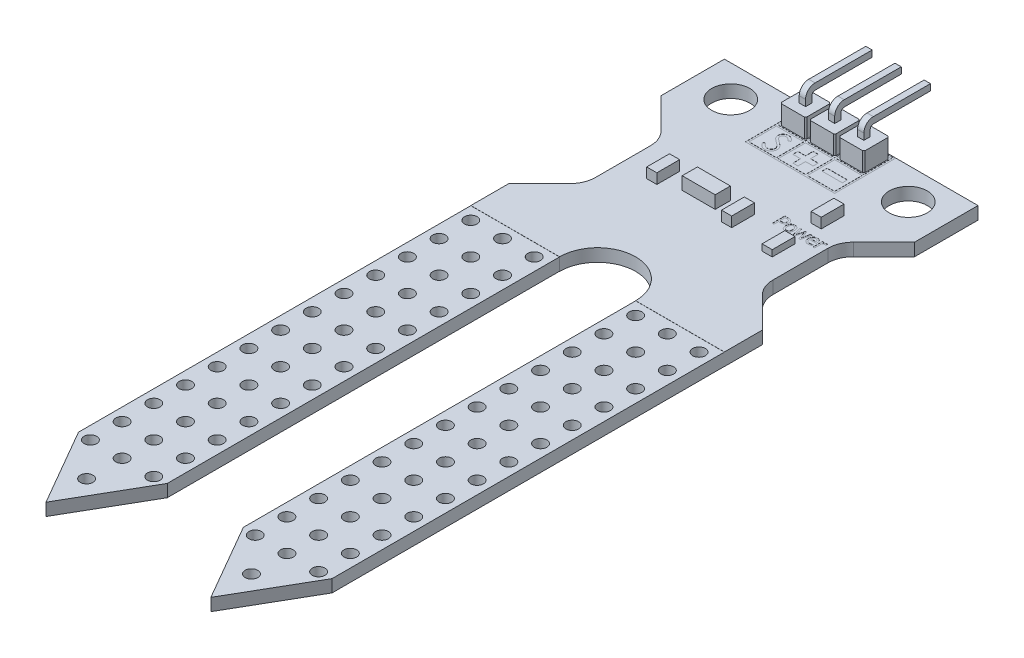
SolidWorks part; units mm, degrees
other "Camera2"
other "Camera4"
ref_plane "Front Plane" through (0, 0, 0) normal (0, 0, 1) x (1, 0, 0)
ref_plane "Top Plane" through (0, 0, 0) normal (0, 1, 0) x (1, 0, 0)
ref_plane "Right Plane" through (0, 0, 0) normal (1, 0, 0) x (0, 0, -1)
sketch "Sketch1" plane through (0, 0, 0) normal (0, 1, 0) x (1, 0, 0)
  line L0 (-10, 0) -> (10, 0)
  line L1 (-10, 0) -> (-10, -57) construction
  line L2 (-10, -57) -> (10, -57) construction
  line L3 (10, -57) -> (10, 0) construction
  line L4 (-10, 0) -> (-10, -5)
  line L5 (-10, -5) -> (-7.5858, -7.4142)
  line L6 (-7, -8.8284) -> (-7, -13.1716)
  line L7 (-7, -11) -> (-10, -11) construction
  line L8 (-10, -17) -> (-7.5858, -14.5858)
  line L9 (-7, -2.5) -> (7, -2.5) construction
  line L10 (0, 0) -> (0, -2.5) construction
  line L11 (-10, -17) -> (-10, -20)
  line L12 (-10, -20) -> (-3, -20)
  line L13 (10, 0) -> (10, -5)
  line L14 (7, -11) -> (10, -11) construction
  line L15 (10, -20) -> (3, -20)
  line L16 (10, -17) -> (10, -20)
  line L17 (10, -17) -> (7.5858, -14.5858)
  line L18 (7, -8.8284) -> (7, -13.1716)
  line L19 (10, -5) -> (7.5858, -7.4142)
  arc A0 (-7.5858, -7.4142) -> (-7, -8.8284) centre (-9, -8.8284) cw
  arc A1 (-7.5858, -14.5858) -> (-7, -13.1716) centre (-9, -13.1716) ccw
  arc A2 (7.5858, -14.5858) -> (7, -13.1716) centre (9, -13.1716) cw
  arc A3 (7.5858, -7.4142) -> (7, -8.8284) centre (9, -8.8284) ccw
  arc A4 (-3, -20) -> (3, -20) centre (0, -20) cw
  point P4 (0, 0)
  point P19 (0, -2.5)
  point P21 (-10, -2.5)
  dimension "D4" = 14
  dimension "D7" = 2
  dimension "D1" = 20
  dimension "D2" = 57
  dimension "D3" = 5
  dimension "D5" = 12
  dimension "D6" = 45
  dimension "D8" = 3
  dimension "D9" = 7
extrude "Base" add sketch "Sketch1" along normal mid plane 1
sketch "Sketch2" plane through (0, 0.5, 0) normal (0, 1, 0) x (1, 0, 0)
  line L0 (0, 0) -> (0, -17) construction
  line L1 (10, 0) -> (-10, 0) construction
  line L2 (7, -2.5) -> (-7, -2.5) construction
  circle A0 centre (-7, -2.5) radius 1.5
  arc A1 (3, -20) -> (-3, -20) centre (0, -20) ccw construction
  circle A2 centre (7, -2.5) radius 1.5
  point P12 (0, -2.5)
  dimension "D1" = 3
  dimension "D3" = 2.5
  dimension "D2" = 14
extrude "Holes" cut sketch "Sketch2" against normal up to next
sketch "Sketch3" plane through (0, 0, 0) normal (0, 1, 0) x (1, 0, 0)
  line L0 (0, 0) -> (0, -57) construction
  line L1 (-10, -20) -> (-3, -20)
  line L2 (-10, -20) -> (-10, -50.9378)
  line L3 (-10, -50.9378) -> (-6.5, -57)
  line L4 (-6.5, -57) -> (-3, -50.9378)
  line L5 (-3, -50.9378) -> (-3, -20)
  line L6 (-6.5, -20) -> (-6.5, -57) construction
  line L7 (-10, -50.9378) -> (-3, -50.9378) construction
  line L8 (10, -50.9378) -> (3, -50.9378) construction
  line L9 (6.5, -20) -> (6.5, -57) construction
  line L10 (3, -50.9378) -> (3, -20)
  line L11 (6.5, -57) -> (3, -50.9378)
  line L12 (10, -50.9378) -> (6.5, -57)
  line L13 (10, -20) -> (10, -50.9378)
  line L14 (10, -20) -> (3, -20)
  dimension "D1" = 57
  dimension "D2" = 30
extrude "Plate" add sketch "Sketch3" along normal mid plane 0.98
sketch "Sketch4" plane through (0, 0.49, 0) normal (0, 1, 0) x (1, 0, 0)
  line L0 (-9, -21) -> (-4, -21) construction
  line L1 (-9, -21) -> (-9, -23.5) construction
  line L2 (-9, -23.5) -> (-6.5, -23.5) construction
  line L3 (-6.5, -51) -> (-6.5, -53.8) construction
  line L4 (-6.5, -20) -> (-6.5, -21) construction
  line L5 (-3, -20) -> (-10, -20) construction
  line L6 (0, 72.5532) -> (0, -72.5532) construction
  line L7 (6.5, -20) -> (6.5, -21) construction
  line L8 (6.5, -51) -> (6.5, -53.8) construction
  line L9 (9, -23.5) -> (6.5, -23.5) construction
  line L10 (9, -21) -> (9, -23.5) construction
  line L11 (9, -21) -> (4, -21) construction
  circle A0 centre (-9, -21) radius 0.5
  circle A1 centre (-6.5, -21) radius 0.5
  circle A2 centre (-4, -21) radius 0.5
  circle A3 centre (-6.5, -23.5) radius 0.5
  circle A4 centre (-4, -23.5) radius 0.5
  circle A5 centre (-6.5, -26) radius 0.5
  circle A6 centre (-4, -26) radius 0.5
  circle A7 centre (-6.5, -28.5) radius 0.5
  circle A8 centre (-4, -28.5) radius 0.5
  circle A9 centre (-6.5, -31) radius 0.5
  circle A10 centre (-4, -31) radius 0.5
  circle A11 centre (-6.5, -33.5) radius 0.5
  circle A12 centre (-4, -33.5) radius 0.5
  circle A13 centre (-6.5, -36) radius 0.5
  circle A14 centre (-4, -36) radius 0.5
  circle A15 centre (-6.5, -38.5) radius 0.5
  circle A16 centre (-4, -38.5) radius 0.5
  circle A17 centre (-6.5, -41) radius 0.5
  circle A18 centre (-4, -41) radius 0.5
  circle A19 centre (-6.5, -43.5) radius 0.5
  circle A20 centre (-4, -43.5) radius 0.5
  circle A21 centre (-6.5, -46) radius 0.5
  circle A22 centre (-4, -46) radius 0.5
  circle A23 centre (-6.5, -48.5) radius 0.5
  circle A24 centre (-4, -48.5) radius 0.5
  circle A25 centre (-6.5, -51) radius 0.5
  circle A26 centre (-4, -51) radius 0.5
  circle A27 centre (-9, -23.5) radius 0.5
  circle A28 centre (-9, -26) radius 0.5
  circle A29 centre (-9, -28.5) radius 0.5
  circle A30 centre (-9, -31) radius 0.5
  circle A31 centre (-9, -33.5) radius 0.5
  circle A32 centre (-9, -36) radius 0.5
  circle A33 centre (-9, -38.5) radius 0.5
  circle A34 centre (-9, -41) radius 0.5
  circle A35 centre (-9, -43.5) radius 0.5
  circle A36 centre (-9, -46) radius 0.5
  circle A37 centre (-9, -48.5) radius 0.5
  circle A38 centre (-9, -51) radius 0.5
  circle A39 centre (-6.5, -53.8) radius 0.5
  circle A40 centre (6.5, -53.8) radius 0.5
  circle A41 centre (9, -51) radius 0.5
  circle A42 centre (9, -48.5) radius 0.5
  circle A43 centre (9, -46) radius 0.5
  circle A44 centre (9, -43.5) radius 0.5
  circle A45 centre (9, -41) radius 0.5
  circle A46 centre (9, -38.5) radius 0.5
  circle A47 centre (9, -36) radius 0.5
  circle A48 centre (9, -33.5) radius 0.5
  circle A49 centre (9, -31) radius 0.5
  circle A50 centre (9, -28.5) radius 0.5
  circle A51 centre (9, -26) radius 0.5
  circle A52 centre (9, -23.5) radius 0.5
  circle A53 centre (4, -51) radius 0.5
  circle A54 centre (6.5, -51) radius 0.5
  circle A55 centre (4, -48.5) radius 0.5
  circle A56 centre (6.5, -48.5) radius 0.5
  circle A57 centre (4, -46) radius 0.5
  circle A58 centre (6.5, -46) radius 0.5
  circle A59 centre (4, -43.5) radius 0.5
  circle A60 centre (6.5, -43.5) radius 0.5
  circle A61 centre (4, -41) radius 0.5
  circle A62 centre (6.5, -41) radius 0.5
  circle A63 centre (4, -38.5) radius 0.5
  circle A64 centre (6.5, -38.5) radius 0.5
  circle A65 centre (4, -36) radius 0.5
  circle A66 centre (6.5, -36) radius 0.5
  circle A67 centre (4, -33.5) radius 0.5
  circle A68 centre (6.5, -33.5) radius 0.5
  circle A69 centre (4, -31) radius 0.5
  circle A70 centre (6.5, -31) radius 0.5
  circle A71 centre (4, -28.5) radius 0.5
  circle A72 centre (6.5, -28.5) radius 0.5
  circle A73 centre (4, -26) radius 0.5
  circle A74 centre (6.5, -26) radius 0.5
  circle A75 centre (4, -23.5) radius 0.5
  circle A76 centre (6.5, -23.5) radius 0.5
  circle A77 centre (4, -21) radius 0.5
  circle A78 centre (6.5, -21) radius 0.5
  circle A79 centre (9, -21) radius 0.5
  point P89 (0, 0)
  dimension "D1" = 1
  dimension "D8" = 2.8
  dimension "D2" = 5
  dimension "D3" = 1
  dimension "D6" = 2.5
  dimension "D4" = 3
  dimension "D5" = 13
extrude "Plate holes" cut sketch "Sketch4" against normal through all
sketch "Sketch5" plane through (0, 0.5, 0) normal (0, 1, 0) x (1, 0, 0)
  line L0 (-7, -2.5) -> (7, -2.5) construction
  line L1 (-3.2, -0.3) -> (-3.3, -0.4)
  line L2 (-3.2, -0.3) -> (-1.4, -0.3)
  line L3 (-3.3, -0.4) -> (-3.3, -2.2)
  line L4 (-3.2, -2.3) -> (-1.4, -2.3)
  line L5 (-1.3, -0.4) -> (-1.3, -2.2)
  line L6 (-3.3, -0.3) -> (-1.3, -2.3) construction
  line L7 (-3.3, -2.3) -> (-1.3, -0.3) construction
  line L8 (-1.4, -0.3) -> (-1.3, -0.4)
  line L9 (-3.3, -2.2) -> (-3.2, -2.3)
  line L10 (-1.3, -2.2) -> (-1.4, -2.3)
  line L11 (-0.9, -0.3) -> (-1, -0.4)
  line L12 (-0.9, -0.3) -> (0.9, -0.3)
  line L13 (-1, -0.4) -> (-1, -2.2)
  line L14 (-0.9, -2.3) -> (0.9, -2.3)
  line L15 (1, -0.4) -> (1, -2.2)
  line L16 (0.9, -0.3) -> (1, -0.4)
  line L17 (-1, -2.2) -> (-0.9, -2.3)
  line L18 (1, -2.2) -> (0.9, -2.3)
  line L19 (-1, -0.3) -> (1, -2.3) construction
  line L20 (-1, -2.3) -> (1, -0.3) construction
  line L21 (1.4, -0.3) -> (1.3, -0.4)
  line L22 (1.4, -0.3) -> (3.2, -0.3)
  line L23 (1.3, -0.4) -> (1.3, -2.2)
  line L24 (1.4, -2.3) -> (3.2, -2.3)
  line L25 (3.3, -0.4) -> (3.3, -2.2)
  line L26 (3.2, -0.3) -> (3.3, -0.4)
  line L27 (1.3, -2.2) -> (1.4, -2.3)
  line L28 (3.3, -2.2) -> (3.2, -2.3)
  line L29 (1.3, -0.3) -> (3.3, -2.3) construction
  line L30 (1.3, -2.3) -> (3.3, -0.3) construction
  line L31 (0, -2.3) -> (0, -2.5) construction
  point P4 (-2.3, -1.3)
  point P19 (0, -1.3)
  point P32 (2.3, -1.3)
  dimension "D1" = 2
  dimension "D2" = 3
  dimension "D3" = 0.2
  dimension "D8" = 0.3
extrude "Socket" add sketch "Sketch5" along normal blind 1.5
sketch "Sketch6" plane through (0, 2, 0) normal (0, 1, 0) x (1, 0, 0)
  line L0 (-2.3, -1.3) -> (-2.3, -0.3) construction
  line L1 (-2.6, -1.6) -> (-2, -1.6)
  line L2 (-2.6, -1.6) -> (-2.6, -1)
  line L3 (-2.6, -1) -> (-2, -1)
  line L4 (-2, -1.6) -> (-2, -1)
  line L5 (-2.6, -1.6) -> (-2, -1) construction
  line L6 (-2.6, -1) -> (-2, -1.6) construction
  line L8 (-1.4, -0.3) -> (-3.2, -0.3) construction
  line L9 (-2.3, -1.3) -> (-3.3, -1.3) construction
  line L10 (-3.3, -0.4) -> (-3.3, -2.2) construction
  point P0 (-2.3, -1.3)
  dimension "D1" = 0.6
sketch "Sketch7" plane through (0, 0, 0) normal (1, 0, 0) x (0, 0, -1)
  line L0 (-1.3, 2) -> (-1.3, 2.5) construction
  line L1 (-0.4, 2) -> (-2.2, 2) construction
  line L2 (-0.8, 3) -> (3.7, 3) construction
  line L3 (-1.05, 2) -> (-1.05, 2.5)
  line L4 (-0.8, 2.75) -> (3.7, 2.75)
  line L5 (-1.55, 2) -> (-1.55, 2.5)
  line L6 (-0.8, 3.25) -> (3.7, 3.25)
  line L7 (3.7, 3.25) -> (3.7, 2.75)
  line L8 (-1.05, 2) -> (-1.55, 2)
  arc A0 (-0.8, 3) -> (-1.3, 2.5) centre (-0.8, 2.5) ccw construction
  arc A1 (-0.8, 2.75) -> (-1.05, 2.5) centre (-0.8, 2.5) ccw
  arc A2 (-0.8, 3.25) -> (-1.55, 2.5) centre (-0.8, 2.5) ccw
  dimension "D2" = 0.5
  dimension "D1" = 0.5
  dimension "D3" = 5
  dimension "D4" = 0.25
  dimension "D5" = 0.25
extrude "Power pin" add sketch "Sketch7" along normal mid plane 0.5
pattern_linear "LPattern2" count 2 spacing 2.3 along (1, 0, 0) count 2 spacing 2.3 along (-1, 0, 0) of "Power pin"
sketch "Sketch9" plane through (0, 0.5, 0) normal (0, 1, 0) x (1, 0, 0)
  line L0 (-0.2, -3.8) -> (-0.2, -4.4)
  line L1 (-3.38, -2.38) -> (-1.22, -2.38)
  line L2 (-3.38, -2.38) -> (-3.38, -0.22)
  line L3 (-3.38, -0.22) -> (-1.22, -0.22)
  line L4 (-1.22, -2.38) -> (-1.22, -0.22)
  line L5 (-3.2, -2.3) -> (-1.4, -2.3) construction
  line L6 (-1.4, -0.3) -> (-3.2, -0.3) construction
  line L7 (-3.3, -0.4) -> (-3.3, -2.2) construction
  line L8 (-1.08, -2.38) -> (1.08, -2.38)
  line L9 (-1.08, -2.38) -> (-1.08, -0.22)
  line L10 (-1.08, -0.22) -> (1.08, -0.22)
  line L11 (1.08, -2.38) -> (1.08, -0.22)
  line L12 (1.22, -2.38) -> (3.38, -2.38)
  line L13 (1.22, -2.38) -> (1.22, -0.22)
  line L14 (1.22, -0.22) -> (3.38, -0.22)
  line L15 (3.38, -2.38) -> (3.38, -0.22)
  line L16 (-1.08, -4.68) -> (1.08, -4.68)
  line L17 (-1.08, -4.68) -> (-1.08, -2.52)
  line L18 (-1.08, -2.52) -> (1.08, -2.52)
  line L19 (1.08, -4.68) -> (1.08, -2.52)
  line L20 (1.22, -4.68) -> (3.38, -4.68)
  line L21 (1.22, -4.68) -> (1.22, -2.52)
  line L22 (1.22, -2.52) -> (3.38, -2.52)
  line L23 (3.38, -4.68) -> (3.38, -2.52)
  line L24 (-3.38, -4.68) -> (-1.22, -4.68)
  line L25 (-3.38, -4.68) -> (-3.38, -2.52)
  line L26 (-3.38, -2.52) -> (-1.22, -2.52)
  line L27 (-1.22, -4.68) -> (-1.22, -2.52)
  line L28 (-3.38, -0.22) -> (-3.38, -0.08) construction
  line L29 (-3.52, -0.08) -> (3.52, -0.08)
  line L30 (-3.52, -0.08) -> (-3.52, -4.82)
  line L31 (-3.52, -4.82) -> (3.52, -4.82)
  line L32 (3.52, -0.08) -> (3.52, -4.82)
  line L33 (-3.38, -0.22) -> (-3.52, -0.22) construction
  line L34 (-3.38, -4.68) -> (-3.38, -4.82) construction
  line L35 (3.38, -0.22) -> (3.52, -0.22) construction
  line L37 (1.5, -3.4) -> (1.5, -3.8)
  line L38 (1.5, -3.8) -> (3.1, -3.8)
  line L39 (3.1, -3.8) -> (3.1, -3.4)
  line L40 (3.1, -3.4) -> (1.5, -3.4)
  line L41 (-0.8, -3.4) -> (-0.8, -3.8)
  line L42 (-0.8, -3.8) -> (-0.2, -3.8)
  line L43 (0.8, -3.8) -> (0.8, -3.4)
  line L44 (0.8, -3.4) -> (0.2, -3.4)
  line L45 (-0.2, -2.8) -> (0.2, -2.8)
  line L46 (-0.2, -2.8) -> (-0.2, -3.4)
  line L47 (-0.2, -4.4) -> (0.2, -4.4)
  line L48 (0.2, -2.8) -> (0.2, -3.4)
  line L49 (-0.2, -3.4) -> (-0.8, -3.4)
  line L50 (0.2, -3.8) -> (0.2, -4.4)
  line L51 (0.2, -3.8) -> (0.8, -3.8)
  line L52 (3.3426, -8.9613) -> (3.2278, -8.9613)
  line L53 (3.2278, -8.9613) -> (3.2278, -9.3284)
  line L54 (3.2278, -9.3284) -> (3.1013, -9.3284)
  line L55 (3.1013, -9.3284) -> (3.1013, -8.3284)
  line L56 (3.1013, -8.3284) -> (3.353, -8.3284)
  line L57 (3.3402, -8.4424) -> (3.2278, -8.4424)
  line L58 (3.2278, -8.4424) -> (3.2278, -8.8474)
  line L59 (3.2278, -8.8474) -> (3.3202, -8.8474)
  line L60 (5.4937, -8.5816) -> (5.3072, -9.3284)
  line L61 (5.3072, -9.3284) -> (5.1926, -9.3284)
  line L62 (5.1926, -9.3284) -> (5.0127, -8.7527)
  line L63 (5.0127, -8.7527) -> (4.8341, -9.3284)
  line L64 (4.8341, -9.3284) -> (4.7201, -9.3284)
  line L65 (4.7201, -9.3284) -> (4.5316, -8.5816)
  line L66 (4.5316, -8.5816) -> (4.6622, -8.5816)
  line L67 (4.6622, -8.5816) -> (4.7905, -9.1599)
  line L68 (4.7905, -9.1599) -> (4.9652, -8.5816)
  line L69 (4.9652, -8.5816) -> (5.0674, -8.5816)
  line L70 (5.0674, -8.5816) -> (5.2466, -9.1599)
  line L71 (5.2466, -9.1599) -> (5.3631, -8.5816)
  line L72 (5.3631, -8.5816) -> (5.4937, -8.5816)
  line L73 (6.2025, -8.8935) -> (6.2025, -8.9613)
  line L74 (6.2025, -8.9613) -> (5.6835, -8.9613)
  line L75 (6.1826, -9.1386) -> (6.1899, -9.1386)
  line L76 (6.1899, -9.1386) -> (6.1899, -9.2782)
  line L77 (5.6835, -8.8601) -> (6.0759, -8.8601)
  line L78 (6.7215, -8.7082) -> (6.715, -8.7082)
  line L79 (6.4557, -8.7962) -> (6.4557, -9.3284)
  line L80 (6.4557, -9.3284) -> (6.3291, -9.3284)
  line L81 (6.3291, -9.3284) -> (6.3291, -8.5816)
  line L82 (6.3291, -8.5816) -> (6.4557, -8.5816)
  line L83 (6.4557, -8.5816) -> (6.4557, -8.6925)
  line L84 (6.7215, -8.5853) -> (6.7215, -8.7082)
  line L85 (-2.7938, -4.1828) -> (-2.6417, -4.0915)
  line L86 (-1.7554, -2.9885) -> (-1.9014, -3.0992)
  spline S0 degree 3 poles (3.7342, -8.6326) (3.7344, -8.6541) (3.7312, -8.6861) (3.7215, -8.7275) (3.7111, -8.7571) (3.6985, -8.7853) (3.678, -8.8198) (3.6595, -8.8432) (3.6454, -8.8569) knots 0 0 0 0 0.260382 0.387742 0.514624 0.640166 0.761611 1 1 1 1
  spline S1 degree 3 poles (3.6454, -8.8569) (3.6282, -8.8742) (3.5993, -8.8968) (3.5564, -8.9209) (3.5216, -8.936) (3.4831, -8.9475) (3.4234, -8.9589) (3.3757, -8.9613) (3.3426, -8.9613) knots 0 0 0 0 0.221352 0.332954 0.446759 0.566652 0.698228 1 1 1 1
  spline S2 degree 3 poles (3.353, -8.3284) (3.3806, -8.3286) (3.4203, -8.3298) (3.4708, -8.3364) (3.504, -8.3429) (3.5348, -8.3514) (3.5726, -8.3658) (3.5988, -8.3803) (3.6149, -8.3915) knots 0 0 0 0 0.301816 0.435226 0.557564 0.673138 0.784559 1 1 1 1
  spline S3 degree 3 poles (3.6149, -8.3915) (3.6332, -8.404) (3.6584, -8.4259) (3.6857, -8.4609) (3.7033, -8.4893) (3.7173, -8.5207) (3.7309, -8.5683) (3.7342, -8.6065) (3.7342, -8.6326) knots 0 0 0 0 0.236653 0.354095 0.472429 0.593575 0.720488 1 1 1 1
  spline S4 degree 3 poles (3.5949, -8.6358) (3.5948, -8.6193) (3.5931, -8.5951) (3.5852, -8.5648) (3.5772, -8.5443) (3.567, -8.5256) (3.5496, -8.5031) (3.5337, -8.4887) (3.5216, -8.4811) knots 0 0 0 0 0.276791 0.40364 0.52478 0.643556 0.760318 1 1 1 1
  spline S5 degree 3 poles (3.5216, -8.4811) (3.5108, -8.4736) (3.4927, -8.465) (3.4672, -8.456) (3.4461, -8.4509) (3.4232, -8.4469) (3.3877, -8.4431) (3.3597, -8.4425) (3.3402, -8.4424) knots 0 0 0 0 0.208675 0.317736 0.431465 0.554189 0.688523 1 1 1 1
  spline S6 degree 3 poles (3.3202, -8.8474) (3.345, -8.8475) (3.3804, -8.8462) (3.4247, -8.8404) (3.4525, -8.8348) (3.4773, -8.8269) (3.5069, -8.813) (3.5261, -8.7981) (3.5374, -8.7869) knots 0 0 0 0 0.321499 0.457599 0.578008 0.68845 0.794252 1 1 1 1
  spline S7 degree 3 poles (3.5374, -8.7869) (3.5471, -8.7772) (3.5599, -8.7612) (3.5734, -8.7381) (3.5815, -8.7202) (3.5877, -8.7012) (3.5936, -8.6731) (3.595, -8.6509) (3.5949, -8.6358) knots 0 0 0 0 0.248146 0.366465 0.48252 0.601376 0.726647 1 1 1 1
  spline S8 degree 3 poles (4.4684, -8.9554) (4.4684, -8.9855) (4.4659, -9.0294) (4.4562, -9.0856) (4.4463, -9.124) (4.4336, -9.1597) (4.4176, -9.1926) (4.399, -9.2228) (4.3776, -9.2501) (4.3538, -9.2745) (4.328, -9.2959) (4.3001, -9.3137) (4.2705, -9.3285) (4.2389, -9.3398) (4.1934, -9.3507) (4.1577, -9.3539) (4.1335, -9.3537) knots 0 0 0 0 0.153334 0.223622 0.290634 0.354958 0.416591 0.476661 0.53556 0.593318 0.64991 0.70585 0.761767 0.818223 0.876674 1 1 1 1
  spline S9 degree 3 poles (4.1335, -9.3537) (4.1086, -9.354) (4.0722, -9.3506) (4.0256, -9.3395) (3.9936, -9.3274) (3.9635, -9.3124) (3.9356, -9.2939) (3.91, -9.2719) (3.8864, -9.2468) (3.8656, -9.2187) (3.8472, -9.1882) (3.8318, -9.1552) (3.8191, -9.1199) (3.8096, -9.0821) (3.7997, -9.0273) (3.7976, -8.9845) (3.7975, -8.9554) knots 0 0 0 0 0.126624 0.185762 0.243469 0.300245 0.356694 0.413633 0.472086 0.531601 0.591562 0.653162 0.716692 0.782593 0.851506 1 1 1 1
  spline S10 degree 3 poles (3.7975, -8.9554) (3.7974, -8.9255) (3.7998, -8.8818) (3.8099, -8.8258) (3.8199, -8.7875) (3.8327, -8.7518) (3.8488, -8.7188) (3.8676, -8.6884) (3.8892, -8.6608) (3.9134, -8.6364) (3.9393, -8.6148) (3.9673, -8.5967) (3.9969, -8.5816) (4.0286, -8.5706) (4.0739, -8.5591) (4.1095, -8.5563) (4.1335, -8.5563) knots 0 0 0 0 0.152158 0.222426 0.289447 0.353383 0.415396 0.47586 0.535165 0.593567 0.650568 0.706628 0.762633 0.819341 0.87748 1 1 1 1
  spline S11 degree 3 poles (4.1335, -8.5563) (4.1577, -8.5561) (4.1934, -8.5593) (4.239, -8.5702) (4.2705, -8.5818) (4.3001, -8.5967) (4.328, -8.6148) (4.3539, -8.6361) (4.3776, -8.6607) (4.399, -8.6882) (4.4177, -8.7185) (4.4335, -8.7514) (4.4464, -8.7871) (4.4562, -8.8254) (4.4658, -8.8816) (4.4685, -8.9255) (4.4684, -8.9554) knots 0 0 0 0 0.123252 0.181668 0.238205 0.294238 0.350327 0.406885 0.464849 0.523978 0.584011 0.64591 0.70988 0.776851 0.847428 1 1 1 1
  spline S12 degree 3 poles (4.3418, -8.9554) (4.3418, -8.9328) (4.3406, -8.9) (4.3344, -8.8581) (4.3289, -8.8299) (4.3211, -8.8041) (4.3119, -8.7806) (4.3007, -8.7595) (4.2882, -8.7406) (4.2737, -8.7241) (4.2581, -8.7094) (4.2407, -8.6974) (4.2221, -8.6873) (4.202, -8.6796) (4.1725, -8.672) (4.1492, -8.6704) (4.1335, -8.6702) knots 0 0 0 0 0.168865 0.245064 0.316508 0.383414 0.446027 0.505125 0.561591 0.615756 0.66878 0.721159 0.77321 0.826581 0.882058 1 1 1 1
  spline S13 degree 3 poles (4.1335, -8.6702) (4.1177, -8.6705) (4.0943, -8.672) (4.0648, -8.6796) (4.0445, -8.6873) (4.0257, -8.6973) (4.0083, -8.7095) (3.9925, -8.7241) (3.9779, -8.7405) (3.9653, -8.7595) (3.9541, -8.7806) (3.9446, -8.8041) (3.9372, -8.83) (3.9313, -8.8581) (3.9253, -8.9) (3.924, -8.9328) (3.9241, -8.9554) knots 0 0 0 0 0.118168 0.173523 0.227235 0.279605 0.331868 0.385137 0.439506 0.495848 0.554814 0.617473 0.684091 0.755478 0.831508 1 1 1 1
  spline S14 degree 3 poles (3.9241, -8.9554) (3.924, -8.9773) (3.9254, -9.0093) (3.9314, -9.0502) (3.9372, -9.0779) (3.9446, -9.1037) (3.9542, -9.127) (3.9653, -9.1484) (3.9779, -9.1677) (3.9924, -9.1847) (4.0083, -9.1996) (4.0258, -9.2119) (4.0444, -9.2223) (4.0647, -9.2302) (4.0943, -9.2377) (4.1177, -9.2398) (4.1335, -9.2398) knots 0 0 0 0 0.164255 0.239131 0.309846 0.376265 0.439182 0.498828 0.556224 0.611938 0.665761 0.718524 0.771581 0.825693 0.881275 1 1 1 1
  spline S15 degree 3 poles (4.1335, -9.2398) (4.1492, -9.2396) (4.1723, -9.2379) (4.2017, -9.2305) (4.2216, -9.2224) (4.2403, -9.2126) (4.2575, -9.2003) (4.2734, -9.1858) (4.2877, -9.169) (4.3007, -9.1502) (4.3117, -9.1289) (4.3209, -9.1053) (4.3286, -9.0796) (4.3345, -9.0517) (4.3405, -9.0102) (4.3418, -8.9777) (4.3418, -8.9554) knots 0 0 0 0 0.117813 0.172983 0.22624 0.278888 0.331025 0.384578 0.439285 0.496204 0.555922 0.618729 0.685842 0.756642 0.832586 1 1 1 1
  spline S16 degree 3 poles (5.9337, -9.3411) (5.9055, -9.3412) (5.8641, -9.3381) (5.8111, -9.3279) (5.775, -9.3167) (5.7412, -9.3027) (5.7101, -9.2851) (5.6813, -9.2647) (5.6553, -9.241) (5.6322, -9.2144) (5.6118, -9.1852) (5.5948, -9.1532) (5.581, -9.1185) (5.57, -9.0813) (5.5596, -9.0266) (5.5571, -8.9838) (5.557, -8.9546) knots 0 0 0 0 0.138011 0.202055 0.263381 0.322416 0.38038 0.437398 0.494395 0.551685 0.609308 0.668092 0.728495 0.79127 0.85721 1 1 1 1
  spline S17 degree 3 poles (5.557, -8.9546) (5.5572, -8.9257) (5.5594, -8.8831) (5.5697, -8.8286) (5.5802, -8.791) (5.5936, -8.7557) (5.6101, -8.7227) (5.6296, -8.692) (5.6519, -8.6639) (5.6768, -8.6387) (5.7036, -8.6166) (5.7323, -8.5978) (5.7628, -8.5826) (5.7953, -8.5708) (5.8417, -8.5592) (5.8783, -8.5565) (5.9029, -8.5563) knots 0 0 0 0 0.146259 0.214368 0.279724 0.343168 0.404962 0.465739 0.526162 0.585964 0.644156 0.701412 0.75874 0.816144 0.875498 1 1 1 1
  spline S18 degree 3 poles (5.9029, -8.5563) (5.9248, -8.5562) (5.9569, -8.5583) (5.9978, -8.567) (6.0259, -8.5756) (6.0519, -8.5873) (6.085, -8.606) (6.1064, -8.6252) (6.1197, -8.6388) knots 0 0 0 0 0.275081 0.402883 0.524391 0.643013 0.760604 1 1 1 1
  spline S19 degree 3 poles (6.1197, -8.6388) (6.1335, -8.6529) (6.151, -8.6774) (6.17, -8.7133) (6.1819, -8.7432) (6.1912, -8.776) (6.2005, -8.8262) (6.2024, -8.866) (6.2025, -8.8935) knots 0 0 0 0 0.215476 0.326952 0.443318 0.566199 0.699559 1 1 1 1
  spline S20 degree 3 poles (5.6835, -8.9613) (5.6834, -8.9817) (5.6853, -9.0114) (5.6924, -9.0494) (5.6994, -9.0752) (5.7087, -9.0991) (5.72, -9.1211) (5.7335, -9.1411) (5.7491, -9.1592) (5.7663, -9.1753) (5.7854, -9.1891) (5.8059, -9.2009) (5.828, -9.2107) (5.8518, -9.2179) (5.8863, -9.2251) (5.9133, -9.2274) (5.9318, -9.2272) knots 0 0 0 0 0.14768 0.215278 0.279761 0.341367 0.400591 0.458795 0.516089 0.572912 0.629707 0.686449 0.744451 0.804022 0.866557 1 1 1 1
  spline S21 degree 3 poles (5.9318, -9.2272) (5.9591, -9.227) (6.012, -9.2213) (6.0623, -9.2043) (6.0856, -9.1943) knots 0 0 0 0 0.518474 1 1 1 1
  spline S22 degree 3 poles (6.0856, -9.1943) (6.1053, -9.1856) (6.1392, -9.1694) (6.17, -9.1482) (6.1826, -9.1386) knots 0 0 0 0 0.577022 1 1 1 1
  spline S23 degree 3 poles (6.1899, -9.2782) (6.1816, -9.2814) (6.1686, -9.2865) (6.1502, -9.2938) (6.1209, -9.3056) (6.096, -9.3149) (6.0759, -9.3203) knots 0 0 0 0 0.218524 0.346372 0.486611 1 1 1 1
  spline S24 degree 3 poles (6.0759, -9.3203) (6.0539, -9.3262) (6.0265, -9.3331) (5.9927, -9.3384) (5.9675, -9.3404) (5.9477, -9.341) (5.9337, -9.3411) knots 0 0 0 0 0.475716 0.586628 0.710511 1 1 1 1
  spline S25 degree 3 poles (6.0759, -8.8601) (6.0758, -8.8446) (6.0738, -8.8223) (6.069, -8.7938) (6.0641, -8.7749) (6.0586, -8.7574) (6.049, -8.7366) (6.0406, -8.7221) (6.0334, -8.7137) knots 0 0 0 0 0.299598 0.432962 0.557938 0.676116 0.788008 1 1 1 1
  spline S26 degree 3 poles (6.0334, -8.7137) (6.0262, -8.7046) (6.0135, -8.6924) (5.9937, -8.6794) (5.9771, -8.6716) (5.9589, -8.6651) (5.9307, -8.6589) (5.9081, -8.6578) (5.8926, -8.6575) knots 0 0 0 0 0.22125 0.334031 0.45002 0.571455 0.703086 1 1 1 1
  spline S27 degree 3 poles (5.8926, -8.6575) (5.8772, -8.6575) (5.8549, -8.6593) (5.8267, -8.6653) (5.808, -8.672) (5.7907, -8.6802) (5.7689, -8.6936) (5.7538, -8.7059) (5.7447, -8.7151) knots 0 0 0 0 0.282218 0.410057 0.529593 0.645 0.761338 1 1 1 1
  spline S28 degree 3 poles (5.7447, -8.7151) (5.7355, -8.7243) (5.7235, -8.7396) (5.7099, -8.7614) (5.7019, -8.7788) (5.695, -8.7971) (5.6882, -8.8242) (5.6844, -8.8454) (5.6835, -8.8601) knots 0 0 0 0 0.242625 0.360813 0.479168 0.599866 0.725826 1 1 1 1
  spline S29 degree 3 poles (6.715, -8.7082) (6.7052, -8.7082) (6.6831, -8.7082) (6.6609, -8.7082) (6.6485, -8.7082) knots 0 0 0 0 0.440476 1 1 1 1
  spline S30 degree 3 poles (6.6485, -8.7082) (6.6318, -8.7082) (6.6064, -8.7111) (6.5734, -8.7203) (6.5486, -8.73) (6.5243, -8.7425) (6.4921, -8.7632) (6.4697, -8.7821) (6.4557, -8.7962) knots 0 0 0 0 0.230943 0.349875 0.471982 0.597666 0.726082 1 1 1 1
  spline S31 degree 3 poles (6.4557, -8.6925) (6.476, -8.6742) (6.5058, -8.6494) (6.546, -8.6216) (6.5728, -8.6067) (6.5982, -8.5954) (6.6306, -8.5852) (6.6552, -8.5815) (6.6715, -8.5816) knots 0 0 0 0 0.33091 0.468651 0.589975 0.700616 0.804235 1 1 1 1
  spline S32 degree 3 poles (6.6715, -8.5816) (6.681, -8.5815) (6.6978, -8.5818) (6.7144, -8.5844) (6.7215, -8.5853) knots 0 0 0 0 0.571302 1 1 1 1
  spline S33 degree 3 poles (-2.6417, -4.0915) (-2.6153, -4.1373) (-2.5737, -4.2014) (-2.5083, -4.2741) (-2.4595, -4.3167) (-2.4089, -4.3502) (-2.3395, -4.3818) (-2.2835, -4.3916) (-2.2465, -4.3915) knots 0 0 0 0 0.304646 0.438547 0.562322 0.677433 0.786897 1 1 1 1
  spline S34 degree 3 poles (-2.2465, -4.3915) (-2.2152, -4.3918) (-2.1685, -4.3863) (-2.1086, -4.369) (-2.0661, -4.3506) (-2.0265, -4.3283) (-1.9917, -4.3014) (-1.9617, -4.2712) (-1.9371, -4.2376) (-1.9182, -4.2014) (-1.8989, -4.152) (-1.8943, -4.1124) (-1.8938, -4.0865) knots 0 0 0 0 0.18093 0.270088 0.360156 0.448343 0.532666 0.613834 0.693982 0.772716 0.849335 1 1 1 1
  spline S35 degree 3 poles (-1.8938, -4.0865) (-1.8937, -4.056) (-1.906, -3.9924) (-1.9388, -3.9366) (-1.9584, -3.9098) knots 0 0 0 0 0.477158 1 1 1 1
  spline S36 degree 3 poles (-1.9584, -3.9098) (-1.975, -3.8879) (-2.003, -3.8547) (-2.0466, -3.8124) (-2.0846, -3.7769) (-2.1279, -3.7407) (-2.1931, -3.6875) (-2.2463, -3.6492) (-2.2829, -3.6228) knots 0 0 0 0 0.18953 0.299198 0.418926 0.548376 0.688136 1 1 1 1
  spline S37 degree 3 poles (-2.2829, -3.6228) (-2.3193, -3.5973) (-2.3703, -3.5595) (-2.434, -3.5102) (-2.4737, -3.4782) (-2.5078, -3.4491) (-2.5433, -3.4173) (-2.5654, -3.3933) (-2.5779, -3.378) knots 0 0 0 0 0.347082 0.495568 0.628357 0.74552 0.845831 1 1 1 1
  spline S38 degree 3 poles (-2.5779, -3.378) (-2.5938, -3.3574) (-2.616, -3.3257) (-2.6397, -3.2806) (-2.6534, -3.2464) (-2.665, -3.2118) (-2.6755, -3.1646) (-2.6786, -3.1282) (-2.6785, -3.1039) knots 0 0 0 0 0.262559 0.388264 0.512667 0.633722 0.755394 1 1 1 1
  spline S39 degree 3 poles (-2.6785, -3.1039) (-2.6786, -3.0663) (-2.6714, -3.0102) (-2.6475, -2.9396) (-2.6227, -2.8901) (-2.5906, -2.8448) (-2.5536, -2.8034) (-2.5095, -2.7685) (-2.461, -2.738) (-2.408, -2.7142) (-2.3334, -2.69) (-2.2742, -2.6844) (-2.235, -2.6838) knots 0 0 0 0 0.16578 0.24628 0.327461 0.408797 0.489715 0.571376 0.655523 0.741019 0.826547 1 1 1 1
  spline S40 degree 3 poles (-2.235, -2.6838) (-2.1928, -2.6838) (-2.1296, -2.6915) (-2.0498, -2.7196) (-2.0017, -2.7434) (-1.9641, -2.7671) (-1.9354, -2.7887) (-1.9064, -2.8136) (-1.8767, -2.8418) (-1.8469, -2.8736) (-1.8052, -2.9219) (-1.775, -2.9609) (-1.7554, -2.9885) knots 0 0 0 0 0.213252 0.31883 0.426794 0.483646 0.543604 0.608308 0.677127 0.750686 0.828713 1 1 1 1
  spline S41 degree 3 poles (-1.9014, -3.0992) (-1.9182, -3.0772) (-1.9435, -3.0462) (-1.9773, -3.0074) (-2.0012, -2.9831) (-2.0236, -2.9611) (-2.0452, -2.9423) (-2.0659, -2.9265) (-2.092, -2.9096) (-2.1248, -2.8929) (-2.1799, -2.8738) (-2.2237, -2.8686) (-2.253, -2.8685) knots 0 0 0 0 0.189629 0.274184 0.352183 0.423199 0.488551 0.548473 0.60144 0.701198 0.799592 1 1 1 1
  spline S42 degree 3 poles (-2.253, -2.8685) (-2.2888, -2.8679) (-2.3413, -2.8756) (-2.4042, -2.9041) (-2.4435, -2.933) (-2.4763, -2.9674) (-2.5082, -3.0202) (-2.5169, -3.066) (-2.5169, -3.0963) knots 0 0 0 0 0.275903 0.402371 0.528414 0.650356 0.765895 1 1 1 1
  spline S43 degree 3 poles (-2.5169, -3.0963) (-2.5175, -3.1157) (-2.5131, -3.1445) (-2.5034, -3.1823) (-2.4919, -3.2105) (-2.4761, -3.239) (-2.4466, -3.2805) (-2.4185, -3.3094) (-2.3983, -3.3289) knots 0 0 0 0 0.214746 0.322939 0.434116 0.553412 0.686073 1 1 1 1
  spline S44 degree 3 poles (-2.3983, -3.3289) (-2.389, -3.3374) (-2.3721, -3.3513) (-2.3453, -3.3713) (-2.3178, -3.3922) (-2.2849, -3.4164) (-2.2304, -3.4552) (-2.1871, -3.4865) (-2.1563, -3.5081) knots 0 0 0 0 0.124952 0.218094 0.333502 0.468789 0.624938 1 1 1 1
  spline S45 degree 3 poles (-2.1563, -3.5081) (-2.1185, -3.5356) (-2.0638, -3.5758) (-1.9964, -3.6317) (-1.9524, -3.671) (-1.9129, -3.7088) (-1.8782, -3.7456) (-1.848, -3.7811) (-1.8155, -3.8267) (-1.7824, -3.8826) (-1.7448, -3.9722) (-1.7323, -4.0427) (-1.7323, -4.089) knots 0 0 0 0 0.187773 0.272396 0.351321 0.424335 0.491909 0.554233 0.611268 0.716348 0.81454 1 1 1 1
  spline S46 degree 3 poles (-1.7323, -4.089) (-1.7318, -4.121) (-1.737, -4.1684) (-1.7523, -4.2296) (-1.7693, -4.2733) (-1.79, -4.3158) (-1.8163, -4.3562) (-1.8468, -4.3952) (-1.8818, -4.4318) (-1.9201, -4.4654) (-1.9606, -4.4953) (-2.0033, -4.5202) (-2.048, -4.5405) (-2.0948, -4.5564) (-2.1606, -4.5721) (-2.212, -4.5763) (-2.2465, -4.5762) knots 0 0 0 0 0.121775 0.18092 0.240256 0.300114 0.361146 0.423501 0.488669 0.553954 0.617581 0.680238 0.742187 0.804663 0.868259 1 1 1 1
  spline S47 degree 3 poles (-2.2465, -4.5762) (-2.2735, -4.5763) (-2.3137, -4.573) (-2.3662, -4.5642) (-2.4041, -4.5538) (-2.4411, -4.5413) (-2.4772, -4.5258) (-2.5123, -4.5072) (-2.5467, -4.4859) (-2.5802, -4.4612) (-2.6126, -4.4324) (-2.6448, -4.4004) (-2.676, -4.3642) (-2.7068, -4.3244) (-2.7477, -4.2645) (-2.7758, -4.2163) (-2.7938, -4.1828) knots 0 0 0 0 0.113696 0.169178 0.224159 0.27872 0.333794 0.389241 0.445822 0.503704 0.564294 0.627975 0.695038 0.765373 0.839611 1 1 1 1
  point P0 (-2.3, -2.38)
  point P9 (-2.3, -2.3)
  point P46 (2.3, -2.52)
  point P49 (2.3, -3.4)
  point P50 (1.5, -3.6)
  point P51 (1.22, -3.6)
  point P57 (-0.8, -3.6)
  point P58 (0, -2.52)
  point P59 (-1.08, -3.6)
  point P66 (0, -2.8)
  dimension "D1" = 0.08
  dimension "D2" = 0.08
  dimension "D3" = 0.14
  dimension "D4" = 3
  dimension "D6" = 0.14
  dimension "D7" = 0.14
  dimension "D10" = 1.6
  dimension "D11" = 0.4
  dimension "D12" = 1.6
  dimension "D13" = 0.4
  dimension "D14" = 1.6
  dimension "D15" = 0.28
  dimension "D16" = 0.28
  dimension "D5" = 2
extrude "Cut-Extrude3" cut sketch "Sketch9" against normal blind 0.01 contours L32 L29 L30 L31 L27 L24 L25 L26 L23 L20 L21 L22 L19 L16 L17 L18 L15 L12 L13 L14 L11 L8 L9 L10 L4 L1 L2 L3 | L50 L51 L43 L44 L48 L45 L46 L49 L41 L42 L0 L47 | L39 L40 L37 L38 | S47 S46 S45 S44 S43 S42 S41 L86 S40 S39 S38 S37 S36 S35 S34 S33 L85 | S3 S2 L56 L55 L54 L53 L52 S1 S0 S7 S6 L59 L58 L57 S5 S4 | S11 S10 S9 S8 S15 S14 S13 S12 | L72 L71 L70 L69 L68 L67 L66 L65 L64 L63 L62 L61 L60 | S24 S23 L76 L75 S22 S21 S20 L74 L73 S19 S18 S17 S16 S28 S27 S26 S25 L77 | S32 S31 L83 L82 L81 L80 L79 S30 S29 L78 L84
sketch "Sketch10" plane through (0, 0.5, 0) normal (0, 1, 0) x (1, 0, 0)
  line L1 (-2.7, -9.4284) -> (-0.1, -9.4284)
  line L2 (-2.7, -9.4284) -> (-2.7, -10.6284)
  line L3 (-2.7, -10.6284) -> (-0.1, -10.6284)
  line L4 (-0.1, -9.4284) -> (-0.1, -10.6284)
  line L5 (-2.7, -9.4284) -> (-0.1, -10.6284) construction
  line L6 (-2.7, -10.6284) -> (-0.1, -9.4284) construction
  point P4 (-1.4, -10.0284)
  point P5 (-2.7, -10.0284)
  dimension "D1" = 2.6
  dimension "D2" = 1.2
  dimension "D3" = 4.3
  dimension "D4" = 1.2
extrude "Big resistor" add sketch "Sketch10" along normal blind 1
sketch "Sketch11" plane through (0, 0.5, 0) normal (0, 1, 0) x (1, 0, 0)
  line L0 (1, -9.4284) -> (1.8, -9.4284)
  line L1 (-4.9, -9.4284) -> (-4.1, -9.4284)
  line L2 (-4.9, -9.4284) -> (-4.9, -11.2284)
  line L3 (-4.9, -11.2284) -> (-4.1, -11.2284)
  line L4 (-4.1, -9.4284) -> (-4.1, -11.2284)
  line L5 (-4.9, -9.4284) -> (-4.1, -11.2284) construction
  line L6 (-4.9, -11.2284) -> (-4.1, -9.4284) construction
  line L7 (1, -9.4284) -> (1, -11.2284)
  line L8 (1, -11.2284) -> (1.8, -11.2284)
  line L9 (1.8, -9.4284) -> (1.8, -11.2284)
  line L10 (1, -9.4284) -> (1.8, -11.2284) construction
  line L11 (1, -11.2284) -> (1.8, -9.4284) construction
  line L12 (4.6163, -5.9816) -> (5.4163, -5.9816)
  line L13 (4.6163, -5.9816) -> (4.6163, -7.7816)
  line L14 (4.6163, -7.7816) -> (5.4163, -7.7816)
  line L15 (5.4163, -5.9816) -> (5.4163, -7.7816)
  line L16 (4.6163, -5.9816) -> (5.4163, -7.7816) construction
  line L17 (4.6163, -7.7816) -> (5.4163, -5.9816) construction
  line L18 (-7, -8.8284) -> (-7, -13.1716) construction
  line L19 (-0.1, -9.4284) -> (-2.7, -9.4284) construction
  line L20 (-0.1, -10.6284) -> (-0.1, -9.4284) construction
  line L21 (4.9652, -8.5816) -> (5.0674, -8.5816) construction
  line L22 (4.9652, -8.5816) -> (5.0674, -8.5816) construction
  point P4 (-4.5, -10.3284)
  point P11 (1.4, -10.3284)
  point P18 (5.0163, -6.8816)
  point P27 (5.0163, -7.7816)
  point P30 (5.0163, -8.5816)
  dimension "D1" = 0.8
  dimension "D2" = 1.8
  dimension "D3" = 0.8
  dimension "D4" = 1.8
  dimension "D5" = 0.8
  dimension "D6" = 1.8
  dimension "D7" = 2.5
  dimension "D8" = 1.5
  dimension "D9" = 0.8
extrude "Small resistor" add sketch "Sketch11" along normal blind 0.8
sketch "Sketch12" plane through (0, 0.5, 0) normal (0, 1, 0) x (1, 0, 0)
  line L0 (7, -13.1716) -> (7, -8.8284) construction
  line L1 (4.6, -9.8284) -> (5.4, -9.8284)
  line L2 (4.6, -9.8284) -> (4.6, -11.6284)
  line L3 (4.6, -11.6284) -> (5.4, -11.6284)
  line L4 (5.4, -9.8284) -> (5.4, -11.6284)
  line L5 (4.6, -9.8284) -> (5.4, -11.6284) construction
  line L6 (4.6, -11.6284) -> (5.4, -9.8284) construction
  line L7 (4.8341, -9.3284) -> (4.7201, -9.3284) construction
  point P4 (5, -10.7284)
  point P7 (7, -11)
  dimension "D1" = 0.8
  dimension "D2" = 1.8
  dimension "D3" = 2
  dimension "D4" = 0.5
extrude "Light" add sketch "Sketch12" along normal blind 0.5
